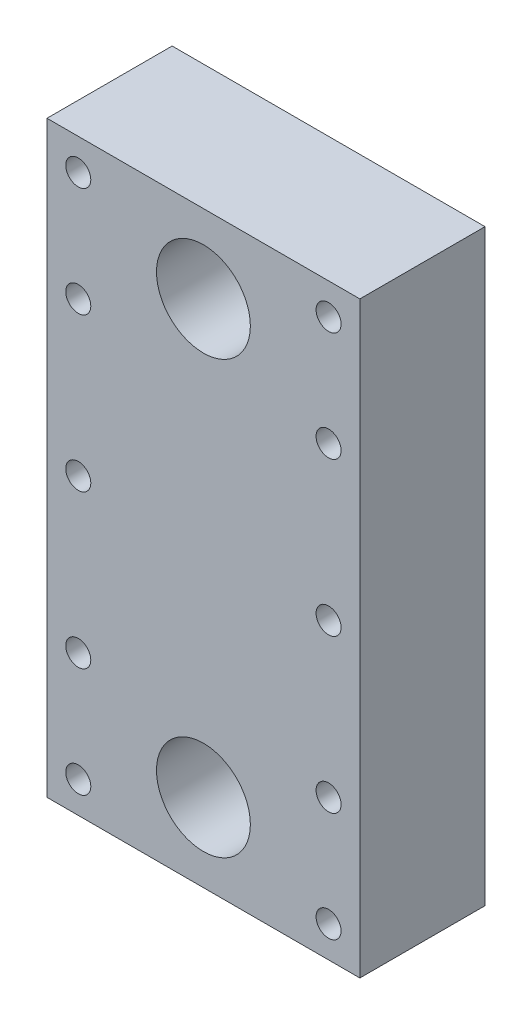
SolidWorks part; units mm, degrees
ref_plane "Front Plane" through (0, 0, 0) normal (0, 0, 1) x (1, 0, 0)
ref_plane "Top Plane" through (0, 0, 0) normal (0, 1, 0) x (1, 0, 0)
ref_plane "Right Plane" through (0, 0, 0) normal (1, 0, 0) x (0, 0, -1)
sketch "Sketch1" plane through (0, 0, 0) normal (0, 0, 1) x (1, 0, 0)
  line L5 (-7, 19) -> (7, 19)
  line L6 (-17, 9) -> (-17, -5)
  line L7 (-7, -15) -> (7, -15)
  line L8 (17, 9) -> (17, -5)
  arc A0 (-7, 19) -> (-17, 9) centre (-7, 9) ccw
  arc A1 (-7, -15) -> (-17, -5) centre (-7, -5) cw
  arc A2 (7, -15) -> (17, -5) centre (7, -5) ccw
  arc A3 (17, 9) -> (7, 19) centre (7, 9) ccw
  point P8 (-17, 19)
  point P11 (-17, -15)
  point P14 (17, -15)
  dimension "D5" = 10
  dimension "D1" = 34
  dimension "D2" = 17
  dimension "D3" = 34
  dimension "D4" = 19
extrude "Boss-Extrude1" add sketch "Sketch1" along normal blind 15
sketch "Sketch2" plane through (0, 0, 0) normal (0, 0, -1) x (-1, 0, 0)
  line L0 (14, 0.39) -> (14, 8.2129)
  line L2 (6.2129, 16) -> (-6.2129, 16)
  line L4 (-14, 8.2129) -> (-14, 0.39)
  line L5 (-14, 0.39) -> (-14, -2.4)
  line L6 (-9, -7.4) -> (-8.25, -7.4)
  line L7 (14, -2.4) -> (14, 0.39)
  line L8 (0, 0) -> (0, 16) construction
  line L10 (6.25, -9.4) -> (6.25, -17.6254)
  line L11 (6.25, -17.6254) -> (-6.25, -17.6254)
  line L12 (-6.25, -9.4) -> (-6.25, -17.6254)
  line L13 (8.25, -7.4) -> (9, -7.4)
  arc A0 (14, 8.2129) -> (6.2129, 16) centre (6.2129, 8.2129) ccw
  arc A1 (-14, 8.2129) -> (-6.2129, 16) centre (-6.2129, 8.2129) cw
  arc A2 (-14, -2.4) -> (-9, -7.4) centre (-9, -2.4) ccw
  arc A3 (14, -2.4) -> (9, -7.4) centre (9, -2.4) cw
  arc A4 (-8.25, -7.4) -> (-6.25, -9.4) centre (-8.25, -9.4) cw
  arc A5 (6.25, -9.4) -> (8.25, -7.4) centre (8.25, -9.4) cw
  point P24 (6.25, -7.4)
  dimension "D3" = 5
  dimension "D4" = 2
  dimension "D1" = 12.5
  dimension "D2" = 6.25
extrude "Cut-Extrude1" cut sketch "Sketch2" against normal through all
sketch "Sketch3" plane through (0, 0, 0) normal (0, 0, -1) x (-1, 0, 0)
  line L0 (0, -0.5076) -> (0, 19) construction
  line L1 (25, -23.0076) -> (-25, -23.0076)
  line L2 (25, -23.0076) -> (25, 21.9924)
  line L3 (25, 21.9924) -> (-25, 21.9924)
  line L4 (-25, -23.0076) -> (-25, 21.9924)
  line L5 (-7, 19) -> (7, 19) construction
  line L6 (0, -0.5076) -> (-19.9583, -0.5076) construction
  line L7 (-6.25, -9.4) -> (-6.25, -15) construction
  line L8 (-9, -7.4) -> (-8.25, -7.4) construction
  line L9 (-14, 8.2129) -> (-14, -2.4) construction
  line L10 (6.2129, 16) -> (-6.2129, 16) construction
  line L11 (14, -2.4) -> (14, 8.2129) construction
  line L12 (8.25, -7.4) -> (9, -7.4) construction
  line L13 (6.25, -9.4) -> (6.25, -15) construction
  line L14 (-6.25, -9.4) -> (-6.25, -15)
  line L15 (-9, -7.4) -> (-8.25, -7.4)
  line L16 (-14, 8.2129) -> (-14, -2.4)
  line L17 (6.2129, 16) -> (-6.2129, 16)
  line L18 (14, -2.4) -> (14, 8.2129)
  line L19 (8.25, -7.4) -> (9, -7.4)
  line L20 (6.25, -9.4) -> (6.25, -15)
  line L21 (6.25, -15) -> (6.25, -17.5)
  line L22 (4.25, -19.5) -> (-4.25, -19.5)
  line L23 (-6.25, -17.5) -> (-6.25, -15)
  arc A0 (-6.25, -9.4) -> (-8.25, -7.4) centre (-8.25, -9.4) ccw construction
  arc A1 (-14, -2.4) -> (-9, -7.4) centre (-9, -2.4) ccw construction
  arc A2 (-6.2129, 16) -> (-14, 8.2129) centre (-6.2129, 8.2129) ccw construction
  arc A3 (14, 8.2129) -> (6.2129, 16) centre (6.2129, 8.2129) ccw construction
  arc A4 (9, -7.4) -> (14, -2.4) centre (9, -2.4) ccw construction
  arc A5 (8.25, -7.4) -> (6.25, -9.4) centre (8.25, -9.4) ccw construction
  arc A6 (-6.25, -9.4) -> (-8.25, -7.4) centre (-8.25, -9.4) ccw
  arc A7 (-14, -2.4) -> (-9, -7.4) centre (-9, -2.4) ccw
  arc A8 (-6.2129, 16) -> (-14, 8.2129) centre (-6.2129, 8.2129) ccw
  arc A9 (14, 8.2129) -> (6.2129, 16) centre (6.2129, 8.2129) ccw
  arc A10 (9, -7.4) -> (14, -2.4) centre (9, -2.4) ccw
  arc A11 (8.25, -7.4) -> (6.25, -9.4) centre (8.25, -9.4) ccw
  arc A12 (-6.25, -17.5) -> (-4.25, -19.5) centre (-4.25, -17.5) ccw
  arc A13 (6.25, -17.5) -> (4.25, -19.5) centre (4.25, -17.5) cw
  dimension "D6" = 2
  dimension "D1" = 45
  dimension "D2" = 50
  dimension "D3" = 25
  dimension "D4" = 22.5
  dimension "D5" = 4.5
extrude "Boss-Extrude3" add sketch "Sketch3" against normal blind 15 contours L2 L1 L4 L3 | L19 A11 L20 L21 A13 L22 A12 L23 L14 A6 L15 A7 L16 A8 L17 A9 L18 A10
sketch "Sketch4" plane through (0, 0, 0) normal (0, 0, -1) x (-1, 0, 0)
  line L0 (6.25, -9.4) -> (6.25, -17.5) construction
  line L1 (6.25, -16.4838) -> (-6.25, -16.4838)
  line L2 (6.25, -16.4838) -> (6.25, -23.0076)
  line L3 (6.25, -23.0076) -> (-6.25, -23.0076)
  line L4 (-6.25, -16.4838) -> (-6.25, -23.0076)
  line L5 (25, -23.0076) -> (-25, -23.0076) construction
  line L6 (-6.25, -9.4) -> (-6.25, -17.5) construction
extrude "Cut-Extrude2" cut sketch "Sketch4" against normal blind 4
fillet "Fillet1" radius 2 2 edges at (-6.25, -23.0076, 2) (6.25, -23.0076, 2)
sketch "Sketch5" plane through (0, 0, 15) normal (0, 0, 1) x (1, 0, 0)
  line L0 (-25, -23.0076) -> (-25, 21.9924) construction
  line L1 (-25, 21.9924) -> (25, 21.9924)
  line L2 (-25, 21.9924) -> (-25, 46.9924)
  line L3 (-25, 46.9924) -> (25, 46.9924)
  line L4 (25, 21.9924) -> (25, 46.9924)
  line L5 (-25, 21.9924) -> (25, 21.9924) construction
  line L6 (25, -23.0076) -> (25, 21.9924) construction
  line L7 (-25, 34.4924) -> (25, 34.4924) construction
  circle A0 centre (0, 34.4924) radius 7.5
  dimension "D2" = 15
  dimension "D1" = 25
extrude "Boss-Extrude4" add sketch "Sketch5" against normal up to surface (15 mm away) up to face at (0, -4.684, 0)
mirror "Mirror1" about plane through (0, 0, 0) normal (0, 1, 0) of "Boss-Extrude4"
sketch "Sketch6" plane through (0, 0, 15) normal (0, 0, 1) x (1, 0, 0)
  line L0 (25, 46.9924) -> (-25, 46.9924) construction
  line L1 (-25, -46.9924) -> (-25, 46.9924) construction
  line L2 (0, 46.9924) -> (0, 43.3154) construction
  line L3 (25, 0) -> (15, 0) construction
  line L4 (25, -46.9924) -> (25, 46.9924) construction
  circle A0 centre (-20, 41.9924) radius 2
  circle A1 centre (20, 41.9924) radius 2
  circle A2 centre (20, -41.9924) radius 2
  circle A3 centre (-20, -41.9924) radius 2
  circle A4 centre (20, 0) radius 2
  circle A5 centre (-20, 0) radius 2
  dimension "D3" = 4
  dimension "D5" = 4
  dimension "D1" = 5
  dimension "D2" = 5
  dimension "D4" = 5
extrude "Cut-Extrude3" cut sketch "Sketch6" against normal through all
sketch "Sketch7" plane through (0, 0, 15) normal (0, 0, 1) x (1, 0, 0)
  line L0 (14, 8.2129) -> (14, -2.4) construction
  line L1 (-6.2129, 16) -> (6.2129, 16) construction
  line L2 (-14, -2.4) -> (-14, 8.2129) construction
  line L3 (-6.25, -17.5) -> (-6.25, -9.4) construction
  line L4 (6.25, -9.4) -> (6.25, -17.5) construction
  line L5 (-4.25, -19.5) -> (4.25, -19.5) construction
  line L6 (-4.25, -19.5) -> (4.25, -19.5)
  line L7 (6.25, -9.4) -> (6.25, -17.5)
  line L8 (-6.25, -17.5) -> (-6.25, -9.4)
  line L9 (-14, -2.4) -> (-14, 8.2129)
  line L10 (-6.2129, 16) -> (6.2129, 16)
  line L11 (14, 8.2129) -> (14, -2.4)
  line L12 (-9, -7.4) -> (-8.25, -7.4)
  line L13 (8.25, -7.4) -> (9, -7.4)
  arc A0 (4.25, -19.5) -> (6.25, -17.5) centre (4.25, -17.5) ccw construction
  arc A1 (14, 8.2129) -> (6.2129, 16) centre (6.2129, 8.2129) ccw construction
  arc A2 (-6.2129, 16) -> (-14, 8.2129) centre (-6.2129, 8.2129) ccw construction
  arc A3 (-14, -2.4) -> (-9, -7.4) centre (-9, -2.4) ccw construction
  arc A4 (9, -7.4) -> (14, -2.4) centre (9, -2.4) ccw construction
  arc A5 (8.25, -7.4) -> (6.25, -9.4) centre (8.25, -9.4) ccw construction
  arc A6 (-6.25, -9.4) -> (-8.25, -7.4) centre (-8.25, -9.4) ccw construction
  arc A7 (-6.25, -17.5) -> (-4.25, -19.5) centre (-4.25, -17.5) ccw construction
  arc A8 (4.25, -19.5) -> (6.25, -17.5) centre (4.25, -17.5) ccw
  arc A9 (-6.25, -17.5) -> (-4.25, -19.5) centre (-4.25, -17.5) ccw
  arc A10 (-6.25, -9.4) -> (-8.25, -7.4) centre (-8.25, -9.4) ccw
  arc A11 (8.25, -7.4) -> (6.25, -9.4) centre (8.25, -9.4) ccw
  arc A12 (9, -7.4) -> (14, -2.4) centre (9, -2.4) ccw
  arc A13 (-14, -2.4) -> (-9, -7.4) centre (-9, -2.4) ccw
  arc A14 (-6.2129, 16) -> (-14, 8.2129) centre (-6.2129, 8.2129) ccw
  arc A15 (14, 8.2129) -> (6.2129, 16) centre (6.2129, 8.2129) ccw
extrude "Boss-Extrude5" add sketch "Sketch7" against normal blind 5
sketch "Sketch8" plane through (0, 0, 15) normal (0, 0, 1) x (1, 0, 0)
  line L0 (25, 46.9924) -> (-25, 46.9924) construction
  line L1 (-25, 46.9924) -> (25, 46.9924)
  line L2 (-25, 46.9924) -> (-25, -46.9924)
  line L3 (-25, -46.9924) -> (25, -46.9924)
  line L4 (25, 46.9924) -> (25, -46.9924)
  line L5 (-25, -46.9924) -> (-25, 46.9924) construction
  line L6 (25, -46.9924) -> (-25, -46.9924) construction
  line L7 (25, -46.9924) -> (25, 46.9924) construction
extrude "Boss-Extrude6" add sketch "Sketch8" along normal blind 5
sketch "Sketch9" plane through (0, 0, 0) normal (0, 0, -1) x (-1, 0, 0)
  circle A0 centre (20, -41.9924) radius 2
  circle A1 centre (0, -34.4924) radius 7.5
  circle A2 centre (-20, -41.9924) radius 2
  circle A3 centre (20, 0) radius 2
  circle A4 centre (-20, 0) radius 2
  circle A5 centre (-20, 41.9924) radius 2
  circle A6 centre (0, 34.4924) radius 7.5
  circle A7 centre (20, 41.9924) radius 2
extrude "Cut-Extrude4" cut sketch "Sketch9" against normal through all
sketch "Sketch10" plane through (0, 0, 20) normal (0, 0, 1) x (1, 0, 0)
  circle A0 centre (-20, 24.4924) radius 2
  circle A1 centre (20, 24.4924) radius 2
  circle A2 centre (20, -24.4924) radius 2
  circle A3 centre (-20, -24.4924) radius 2
extrude "Cut-Extrude5" cut sketch "Sketch10" against normal through all
